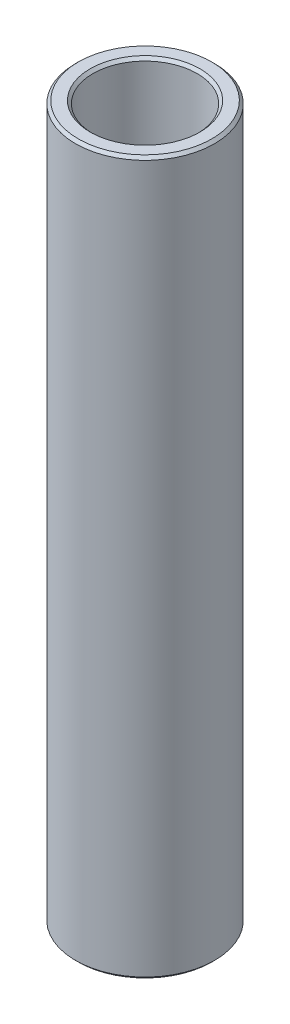
SolidWorks part; units mm, degrees
ref_plane "Front Plane" through (0, 0, 0) normal (0, 0, 1) x (1, 0, 0)
ref_plane "Top Plane" through (0, 0, 0) normal (0, 1, 0) x (1, 0, 0)
ref_plane "Right Plane" through (0, 0, 0) normal (1, 0, 0) x (0, 0, -1)
sketch "Sketch1" plane through (0, 0, 0) normal (0, 0, 1) x (1, 0, 0)
  line L0 (4.7625, 63.2989) -> (4.7625, 128.4343)
  line L1 (4.7625, 128.4343) -> (6.35, 128.4343)
  line L2 (6.35, 128.4343) -> (6.35, 63.2989)
  line L3 (6.35, 63.2989) -> (4.7625, 63.2989)
  line L4 (-10.0875, 72.03) -> (-120.0875, 72.03) construction
  line L6 (0, 53.7739) -> (0, 137.9593) construction
  dimension "D1" = 9.525
  dimension "D2" = 9.525
  dimension "D3" = 12.7
  dimension "D4" = 9.525
revolve "Revolve1" add sketch "Sketch1" angle 360 about L6
chamfer "Chamfer1" distance 0.254 angle 45 4 edges at (6.35, 128.4343, 0) (4.7625, 128.4343, 0) (4.7625, 63.2989, 0) (6.35, 63.2989, 0)
equation "\"D4@Sketch1\"=\"D1@Sketch1\""
